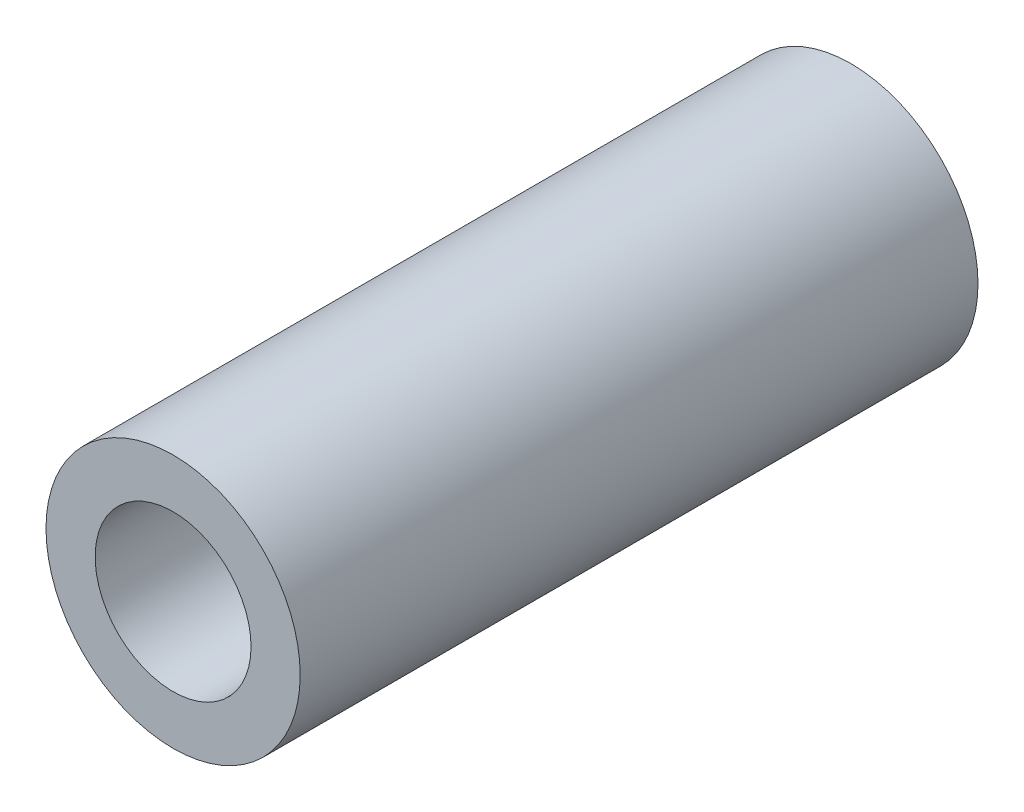
SolidWorks part; units mm, degrees
ref_plane "Front Plane" through (0, 0, 0) normal (0, 0, 1) x (1, 0, 0)
ref_plane "Top Plane" through (0, 0, 0) normal (0, 1, 0) x (1, 0, 0)
ref_plane "Right Plane" through (0, 0, 0) normal (1, 0, 0) x (0, 0, -1)
sketch "Sketch1" plane through (0, 0, 0) normal (0, 0, 1) x (1, 0, 0)
  line L0 (0, 1.4605) -> (0, 2.3813) construction
  line L1 (0, -1.4605) -> (0, -2.3813) construction
  circle A0 centre (0, 0) radius 2.3813
  circle A1 centre (0, 0) radius 1.4605
  dimension "OD" = 4.7625
  dimension "ID" = 2.921
sketch "Sketch2" plane through (0, 0, 0) normal (1, 0, 0) x (0, 0, -1)
  line L0 (-6.35, 1.4605) -> (6.35, 1.4605) construction
  line L1 (-6.35, -1.4605) -> (6.35, -1.4605) construction
  line L2 (-6.35, -2.3813) -> (6.35, -2.3813) construction
  line L3 (-6.35, 2.3813) -> (6.35, 2.3813) construction
  dimension "Length" = 12.7
extrude "Extrude1" add sketch "Sketch1" along normal up to vertex (6.35 mm away) and the other way up to vertex (6.35 mm away) up to point (0, 1.4605, 6.35) other way up to point (0, 1.4605, -6.35)
sketch "Sketch3" plane through (0, 0, 6.35) normal (0, 0, 1) x (1, 0, 0)
  circle A0 centre (0, 0) radius 1.4605 construction
  circle A3 centre (0, 0) radius 1.4605
  point P3 (-1.4605, 0)
